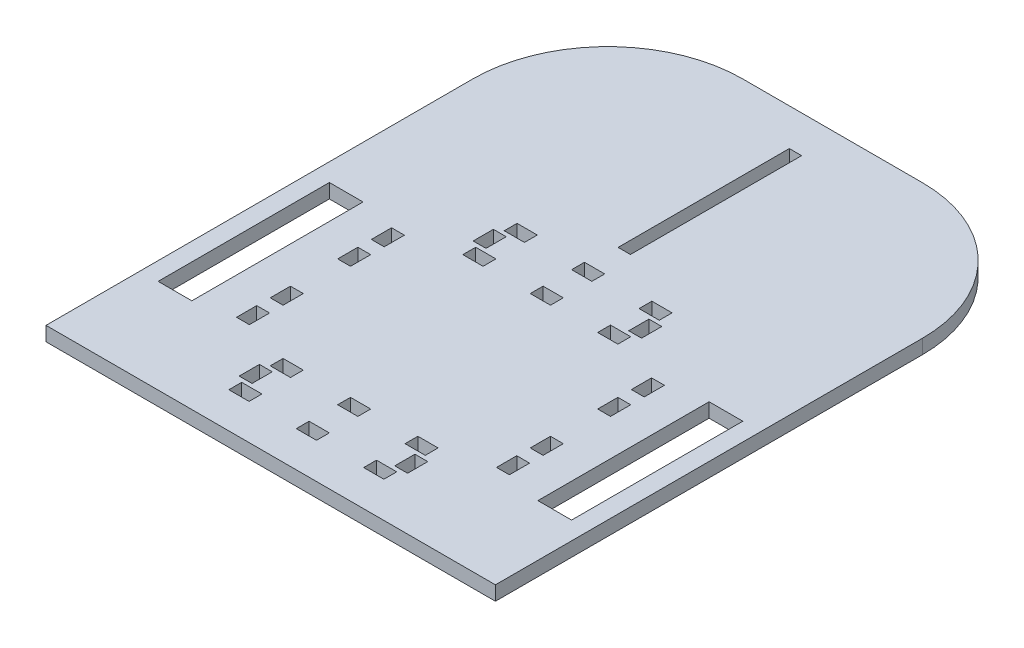
SolidWorks part; units mm, degrees
ref_plane "Front Plane" through (0, 0, 0) normal (0, 0, 1) x (1, 0, 0)
ref_plane "Top Plane" through (0, 0, 0) normal (0, 1, 0) x (1, 0, 0)
ref_plane "Right Plane" through (0, 0, 0) normal (1, 0, 0) x (0, 0, -1)
sketch "Sketch1" plane through (0, 0, 0) normal (0, 1, 0) x (1, 0, 0)
  line L0 (0, 124.3155) -> (0, -124.3155) construction
  line L1 (-100, 125) -> (100, 125)
  line L2 (-100, 125) -> (-100, -125)
  line L3 (-100, -125) -> (100, -125)
  line L4 (100, 125) -> (100, -125)
  line L5 (-100, 125) -> (100, -125) construction
  line L6 (-100, -125) -> (100, 125) construction
  line L8 (-2.7431, 108.5359) -> (2.7431, 108.5359)
  line L9 (-2.7431, 108.5359) -> (-2.7431, 32.3359)
  line L10 (-2.7431, 32.3359) -> (2.7431, 32.3359)
  line L11 (2.7431, 108.5359) -> (2.7431, 32.3359)
  line L12 (-2.7431, 108.5359) -> (2.7431, 32.3359) construction
  line L13 (-2.7431, 32.3359) -> (2.7431, 108.5359) construction
  line L14 (55, -55.5) -> (60.715, -55.5)
  line L15 (55, -55.5) -> (55, -64.5)
  line L16 (55, -64.5) -> (60.715, -64.5)
  line L17 (60.715, -55.5) -> (60.715, -64.5)
  line L18 (55, -55.5) -> (60.715, -64.5) construction
  line L19 (55, -64.5) -> (60.715, -55.5) construction
  line L23 (55, -34.5) -> (60.715, -25.5) construction
  line L24 (55, -25.5) -> (60.715, -25.5)
  line L26 (55, -34.5) -> (55, -25.5)
  line L27 (55, -25.5) -> (60.715, -34.5) construction
  line L28 (-100, 125) -> (-100, -125)
  line L29 (100, 125) -> (100, -125)
  line L36 (60.715, -34.5) -> (60.715, -25.5)
  line L37 (55, -34.5) -> (60.715, -34.5)
  line L39 (10.0381, -45) -> (50010.0381, -45) construction
  line L40 (-4.5, -85) -> (4.5, -85)
  line L41 (-4.5, -85) -> (-4.5, -90.715)
  line L42 (-4.5, -90.715) -> (4.5, -90.715)
  line L43 (4.5, -85) -> (4.5, -90.715)
  line L44 (-4.5, -85) -> (4.5, -90.715) construction
  line L45 (-4.5, -90.715) -> (4.5, -85) construction
  line L46 (-55, -55.5) -> (-60.715, -55.5)
  line L47 (-55, -55.5) -> (-60.715, -64.5) construction
  line L48 (-60.715, -55.5) -> (-60.715, -64.5)
  line L49 (-55, -55.5) -> (-55, -64.5)
  line L50 (-55, -64.5) -> (-60.715, -55.5) construction
  line L51 (-55, -64.5) -> (-60.715, -64.5)
  line L52 (-55, -34.5) -> (-60.715, -34.5)
  line L53 (-55, -34.5) -> (-55, -25.5)
  line L54 (-55, -25.5) -> (-60.715, -34.5) construction
  line L55 (-55, -34.5) -> (-60.715, -25.5) construction
  line L56 (-60.715, -34.5) -> (-60.715, -25.5)
  line L57 (-55, -25.5) -> (-60.715, -25.5)
  line L65 (25.5, -85) -> (34.5, -85)
  line L66 (25.5, -85) -> (25.5, -90.715)
  line L67 (25.5, -90.715) -> (34.5, -90.715)
  line L68 (34.5, -85) -> (34.5, -90.715)
  line L69 (25.5, -85) -> (34.5, -90.715) construction
  line L70 (25.5, -90.715) -> (34.5, -85) construction
  line L75 (-92, -6.9) -> (-77, -6.9)
  line L76 (-92, -6.9) -> (-92, -83.1)
  line L77 (-92, -83.1) -> (-77, -83.1)
  line L82 (-34.5, -85) -> (-34.5, -90.715)
  line L83 (-25.5, -90.715) -> (-34.5, -90.715)
  line L84 (-25.5, -90.715) -> (-34.5, -85) construction
  line L85 (-25.5, -85) -> (-34.5, -90.715) construction
  line L86 (-25.5, -85) -> (-25.5, -90.715)
  line L87 (-25.5, -85) -> (-34.5, -85)
  line L106 (-1044.2796, -85) -> (48955.7204, -85) construction
  line L107 (57.8575, -1064.2749) -> (57.8575, 48935.7251) construction
  line L108 (-1000, -97.065) -> (49000, -97.065) construction
  line L113 (25.5, -103.415) -> (34.5, -103.415)
  line L114 (34.5, -109.13) -> (34.5, -103.415)
  line L115 (25.5, -109.13) -> (34.5, -109.13)
  line L116 (25.5, -109.13) -> (25.5, -103.415)
  line L117 (-4.5, -103.415) -> (4.5, -103.415)
  line L118 (4.5, -109.13) -> (4.5, -103.415)
  line L119 (-4.5, -109.13) -> (4.5, -109.13)
  line L120 (-4.5, -109.13) -> (-4.5, -103.415)
  line L121 (-25.5, -109.13) -> (-34.5, -109.13)
  line L122 (-25.5, -109.13) -> (-25.5, -103.415)
  line L123 (-25.5, -103.415) -> (-34.5, -103.415)
  line L124 (-34.5, -109.13) -> (-34.5, -103.415)
  line L129 (-4.5, 0.715) -> (4.5, 0.715)
  line L130 (4.5, -5) -> (4.5, 0.715)
  line L131 (-4.5, -5) -> (4.5, -5)
  line L132 (-4.5, -5) -> (-4.5, 0.715)
  line L133 (25.5, 0.715) -> (34.5, 0.715)
  line L134 (34.5, -5) -> (34.5, 0.715)
  line L135 (25.5, -5) -> (34.5, -5)
  line L136 (25.5, -5) -> (25.5, 0.715)
  line L145 (25.5, 19.13) -> (25.5, 13.415)
  line L146 (25.5, 19.13) -> (34.5, 19.13)
  line L147 (34.5, 19.13) -> (34.5, 13.415)
  line L148 (25.5, 13.415) -> (34.5, 13.415)
  line L149 (-4.5, 19.13) -> (-4.5, 13.415)
  line L150 (-4.5, 19.13) -> (4.5, 19.13)
  line L151 (4.5, 19.13) -> (4.5, 13.415)
  line L152 (-4.5, 13.415) -> (4.5, 13.415)
  line L153 (-25.5, 19.13) -> (-25.5, 13.415)
  line L154 (-25.5, 13.415) -> (-34.5, 13.415)
  line L155 (-34.5, 19.13) -> (-34.5, 13.415)
  line L156 (-25.5, 19.13) -> (-34.5, 19.13)
  line L157 (-25.5, -5) -> (-34.5, -5)
  line L158 (-25.5, -5) -> (-25.5, 0.715)
  line L159 (-25.5, 0.715) -> (-34.5, 0.715)
  line L160 (-34.5, -5) -> (-34.5, 0.715)
  line L161 (-77, -6.9) -> (-77, -83.1)
  line L162 (-92, -6.9) -> (-77, -83.1) construction
  line L163 (-92, -83.1) -> (-77, -6.9) construction
  line L174 (92, -83.1) -> (77, -83.1)
  line L175 (77, -6.9) -> (77, -83.1)
  line L176 (92, -6.9) -> (77, -6.9)
  line L177 (92, -6.9) -> (92, -83.1)
  line L182 (55, -70.5) -> (60.715, -70.5)
  line L183 (55, -70.5) -> (55, -79.5)
  line L184 (55, -79.5) -> (60.715, -79.5)
  line L185 (60.715, -70.5) -> (60.715, -79.5)
  line L186 (55, -70.5) -> (60.715, -79.5) construction
  line L187 (55, -79.5) -> (60.715, -70.5) construction
  line L188 (-55, -79.5) -> (-60.715, -70.5) construction
  line L189 (-55, -70.5) -> (-60.715, -79.5) construction
  line L190 (-60.715, -70.5) -> (-60.715, -79.5)
  line L191 (-55, -79.5) -> (-60.715, -79.5)
  line L192 (-55, -70.5) -> (-55, -79.5)
  line L193 (-55, -70.5) -> (-60.715, -70.5)
  line L194 (55, -10.5) -> (60.715, -19.5) construction
  line L195 (55, -19.5) -> (60.715, -10.5) construction
  line L196 (60.715, -19.5) -> (60.715, -10.5)
  line L197 (55, -10.5) -> (60.715, -10.5)
  line L198 (55, -19.5) -> (55, -10.5)
  line L199 (55, -19.5) -> (60.715, -19.5)
  line L200 (-55, -19.5) -> (-60.715, -10.5) construction
  line L201 (-55, -10.5) -> (-60.715, -19.5) construction
  line L202 (-55, -19.5) -> (-60.715, -19.5)
  line L203 (-55, -19.5) -> (-55, -10.5)
  line L204 (-55, -10.5) -> (-60.715, -10.5)
  line L205 (-60.715, -19.5) -> (-60.715, -10.5)
  line L206 (-31.75, -101.565) -> (-37.465, -92.565) construction
  line L207 (31.75, -92.565) -> (37.465, -92.565)
  line L208 (31.75, -92.565) -> (31.75, -101.565)
  line L209 (31.75, -101.565) -> (37.465, -101.565)
  line L210 (37.465, -92.565) -> (37.465, -101.565)
  line L211 (31.75, -92.565) -> (37.465, -101.565) construction
  line L212 (31.75, -101.565) -> (37.465, -92.565) construction
  line L213 (-31.75, -92.565) -> (-37.465, -101.565) construction
  line L214 (-37.465, -92.565) -> (-37.465, -101.565)
  line L215 (-31.75, -101.565) -> (-37.465, -101.565)
  line L216 (-31.75, -92.565) -> (-31.75, -101.565)
  line L217 (-31.75, -92.565) -> (-37.465, -92.565)
  line L218 (31.75, 11.565) -> (37.465, 2.565) construction
  line L219 (31.75, 2.565) -> (37.465, 11.565) construction
  line L220 (37.465, 2.565) -> (37.465, 11.565)
  line L221 (31.75, 11.565) -> (37.465, 11.565)
  line L222 (31.75, 2.565) -> (31.75, 11.565)
  line L223 (31.75, 2.565) -> (37.465, 2.565)
  line L224 (-31.75, 2.565) -> (-37.465, 11.565) construction
  line L225 (-31.75, 11.565) -> (-37.465, 2.565) construction
  line L226 (-31.75, 2.565) -> (-37.465, 2.565)
  line L227 (-31.75, 2.565) -> (-31.75, 11.565)
  line L228 (-31.75, 11.565) -> (-37.465, 11.565)
  line L229 (-37.465, 2.565) -> (-37.465, 11.565)
  point P0 (0, 0)
  point P6 (0, 70.4359)
  point P9 (0, 0)
  point P14 (57.8575, -60)
  point P22 (57.8575, -30)
  point P27 (-57.8575, -60)
  point P31 (0, -87.8575)
  point P36 (-57.8575, -30)
  point P41 (0.0096, -59.601)
  point P46 (30, -87.8575)
  point P52 (-84.5, -45)
  point P62 (-47, -45)
  point P67 (-30, -87.8575)
  point P85 (57.8575, -75)
  point P122 (-57.8575, -75)
  point P127 (57.8575, -15)
  point P132 (-57.8575, -15)
  point P133 (34.6075, -97.065)
  point P141 (-34.6075, -97.065)
  point P146 (34.6075, 7.065)
  point P151 (-34.6075, 7.065)
  point P152 (-47, -45)
  point P153 (-47, -45)
  point P154 (0, 0)
  dimension "D1" = 9
  dimension "D4" = 9
  dimension "D5" = 9
  dimension "D12" = 80
  dimension "D8" = 55
  dimension "D10" = 8
  dimension "D13" = 200
  dimension "D14" = 250
  dimension "D15" = 76.2
  dimension "D16" = 15
  dimension "D3" = 5.715
  dimension "D7" = 5.715
  dimension "D20" = 12.7
  dimension "D21" = 76.2
  dimension "D6" = 30
  dimension "D22" = 15
  dimension "D9" = 40
  dimension "D11" = 5.715
  dimension "D23" = 9
  dimension "D24" = 5.715
  dimension "D25" = 15
  dimension "D26" = 9
  dimension "D27" = 5.715
  dimension "D28" = 31.75
extrude "Boss-Extrude1" add sketch "Sketch1" along normal blind 6.35
fillet "Fillet1" radius 60 2 edges at (100, 3.175, -125) (-100, 3.175, -125)
equation "\"toothBaseWidth\"=0.01"
equation "\"toothEndWidth\"=0.009"
equation "\"toothLength\"= 0.005715"
equation "\"holeWidth\" = 0.009"
equation "\"motorHolderToothSeparation\" = 0.01"
equation "\"magnetHolderToothSeparation\" = 0.02"
equation "\"D5@Sketch1\"= \"holeWidth\""
equation "\"D4@Sketch1\"= \"holeWidth\""
equation "\"magnetWidth\" = 0.0127"
equation "\"quarterInch\" = 0.005715"
equation "\"coilThickness\" = 0.0254"
equation "\"coilOuterDiameter\" = 0.0508"
equation "\"legoThickness\" = 0.008"
equation "\"legoWidth\" = 0.016"
equation "\"D10@Sketch1\"= \"legoThickness\""
equation "\"D3@Sketch1\"=\"quarterInch\""
equation "\"D7@Sketch1\"=\"quarterInch\""
equation "\"D1@Sketch1\"=\"holeWidth\""
equation "\"D11@Sketch1\"=\"quarterInch\""
equation "\"D24@Sketch1\"=\"quarterInch\""
equation "\"D23@Sketch1\"=\"holeWidth\""
equation "\"D26@Sketch1\"=\"holeWidth\""
equation "\"D27@Sketch1\"=\"quarterInch\""
